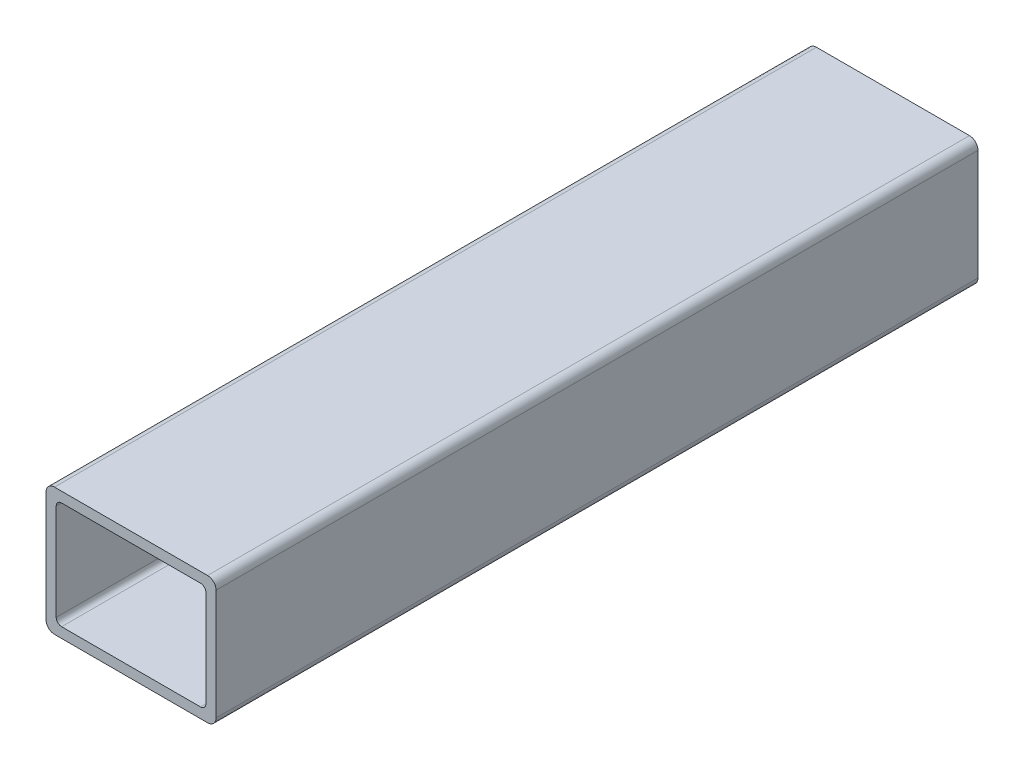
SolidWorks part; units mm, degrees
material "Plain Carbon Steel"
ref_plane "Front" through (0, 0, 0) normal (0, 0, 1) x (1, 0, 0)
ref_plane "Top" through (0, 0, 0) normal (0, 1, 0) x (1, 0, 0)
ref_plane "Right" through (0, 0, 0) normal (1, 0, 0) x (0, 0, -1)
sketch "Sketch1" plane through (0, 0, 0) normal (0, 0, 1) x (1, 0, 0)
  line L0 (-22.352, 0) -> (-25.4, 0) construction
  line L1 (22.86, -19.05) -> (-22.86, -19.05)
  line L2 (25.4, -16.51) -> (25.4, 16.51)
  line L3 (22.86, 19.05) -> (-22.86, 19.05)
  line L4 (-25.4, -16.51) -> (-25.4, 16.51)
  line L5 (25.4, -19.05) -> (-25.4, 19.05) construction
  line L6 (25.4, 19.05) -> (-25.4, -19.05) construction
  line L7 (20.7518, 16.002) -> (-20.7518, 16.002)
  line L8 (22.352, 14.4018) -> (22.352, -14.4018)
  line L9 (20.7518, -16.002) -> (-20.7518, -16.002)
  line L10 (-22.352, 14.4018) -> (-22.352, -14.4018)
  line L11 (22.352, 16.002) -> (-22.352, -16.002) construction
  line L12 (22.352, -16.002) -> (-22.352, 16.002) construction
  line L13 (0, -16.002) -> (0, -19.05) construction
  line L14 (22.352, -14.4018) -> (22.352, -19.05) construction
  line L16 (22.352, -19.05) -> (25.4, -19.05) construction
  arc A0 (-20.7518, -16.002) -> (-22.352, -14.4018) centre (-20.7518, -14.4018) cw
  arc A1 (22.352, -14.4018) -> (20.7518, -16.002) centre (20.7518, -14.4018) cw
  arc A2 (20.7518, 16.002) -> (22.352, 14.4018) centre (20.7518, 14.4018) cw
  arc A3 (-20.7518, 16.002) -> (-22.352, 14.4018) centre (-20.7518, 14.4018) ccw
  arc A4 (22.86, -19.05) -> (25.4, -16.51) centre (22.86, -16.51) ccw
  arc A5 (25.4, 16.51) -> (22.86, 19.05) centre (22.86, 16.51) ccw
  arc A6 (-22.86, 19.05) -> (-25.4, 16.51) centre (-22.86, 16.51) ccw
  arc A7 (-22.86, -19.05) -> (-25.4, -16.51) centre (-22.86, -16.51) cw
  point P0 (0, 0)
  point P6 (0, 0)
  dimension "D2" = 1.6002
  dimension "D3" = 2.54
sketch "Sketch2" plane through (0, 0, 0) normal (1, 0, 0) x (0, 0, -1)
  line L0 (-152.4, 0) -> (152.4, 0) construction
  dimension "Length" = 304.8
ref_plane "Plane1" through (25.4, 0, 0) normal (1, 0, 0) x (0, 0, -1)
sketch "Sketch5" plane through (25.4, 0, 0) normal (1, 0, 0) x (0, 0, -1)
  line L0 (-152.4, 19.05) -> (-152.4, -19.05) construction
  line L1 (152.4, 19.05) -> (152.4, -19.05) construction
sketch "Sketch4" plane through (0, 0, 0) normal (0, 0, 1) x (1, 0, 0)
  line L0 (25.4, -16.51) -> (25.4, 16.51) construction
  line L1 (22.86, 19.05) -> (-22.86, 19.05) construction
  line L2 (-25.4, -16.51) -> (-25.4, 16.51) construction
  line L3 (22.86, -19.05) -> (-22.86, -19.05) construction
  line L4 (22.352, 14.4018) -> (22.352, -14.4018) construction
  line L5 (20.7518, -16.002) -> (-20.7518, -16.002) construction
  line L6 (-22.352, 14.4018) -> (-22.352, -14.4018) construction
  line L7 (20.7518, 16.002) -> (-20.7518, 16.002) construction
  line L8 (25.4, -16.51) -> (25.4, 16.51)
  line L9 (22.86, 19.05) -> (-22.86, 19.05)
  line L10 (-25.4, -16.51) -> (-25.4, 16.51)
  line L11 (22.86, -19.05) -> (-22.86, -19.05)
  line L12 (22.352, 14.4018) -> (22.352, -14.4018)
  line L13 (20.7518, -16.002) -> (-20.7518, -16.002)
  line L14 (-22.352, 14.4018) -> (-22.352, -14.4018)
  line L15 (20.7518, 16.002) -> (-20.7518, 16.002)
  arc A0 (25.4, 16.51) -> (22.86, 19.05) centre (22.86, 16.51) ccw construction
  arc A1 (-22.86, 19.05) -> (-25.4, 16.51) centre (-22.86, 16.51) ccw construction
  arc A2 (-25.4, -16.51) -> (-22.86, -19.05) centre (-22.86, -16.51) ccw construction
  arc A3 (22.86, -19.05) -> (25.4, -16.51) centre (22.86, -16.51) ccw construction
  arc A4 (20.7518, -16.002) -> (22.352, -14.4018) centre (20.7518, -14.4018) ccw construction
  arc A5 (-22.352, -14.4018) -> (-20.7518, -16.002) centre (-20.7518, -14.4018) ccw construction
  arc A6 (-20.7518, 16.002) -> (-22.352, 14.4018) centre (-20.7518, 14.4018) ccw construction
  arc A7 (22.352, 14.4018) -> (20.7518, 16.002) centre (20.7518, 14.4018) ccw construction
  arc A8 (25.4, 16.51) -> (22.86, 19.05) centre (22.86, 16.51) ccw
  arc A9 (-22.86, 19.05) -> (-25.4, 16.51) centre (-22.86, 16.51) ccw
  arc A10 (-25.4, -16.51) -> (-22.86, -19.05) centre (-22.86, -16.51) ccw
  arc A11 (22.86, -19.05) -> (25.4, -16.51) centre (22.86, -16.51) ccw
  arc A12 (20.7518, -16.002) -> (22.352, -14.4018) centre (20.7518, -14.4018) ccw
  arc A13 (-22.352, -14.4018) -> (-20.7518, -16.002) centre (-20.7518, -14.4018) ccw
  arc A14 (-20.7518, 16.002) -> (-22.352, 14.4018) centre (-20.7518, 14.4018) ccw
  arc A15 (22.352, 14.4018) -> (20.7518, 16.002) centre (20.7518, 14.4018) ccw
extrude "Boss-Extrude1" add sketch "Sketch4" along normal blind 227.5637
sketch "Sketch6" plane through (0, 19.05, 0) normal (0, 1, 0) x (1, 0, 0)
  line L0 (0, -227.5637) -> (0, -183.6318) construction
  line L2 (-22.86, -183.6318) -> (22.86, -183.6318) construction
  line L3 (-22.86, 0) -> (-22.86, -227.5637) construction
  line L4 (22.86, 0) -> (22.86, -227.5637) construction
  line L5 (-22.86, -43.9318) -> (22.86, -43.9318) construction
  line L6 (22.86, -227.5637) -> (-22.86, -227.5637) construction
  line L7 (0, -183.6318) -> (0, -43.9318) construction
  line L8 (0, -43.9318) -> (0, 0) construction
  line L9 (22.86, 0) -> (-22.86, 0) construction
  dimension "D1" = 139.7
equation "\"D3@Sketch1\"=\"Outside Width@Sketch1\"*.05"
equation "\"D2@Sketch1\"=\"D1@Sketch1\"*.05"
